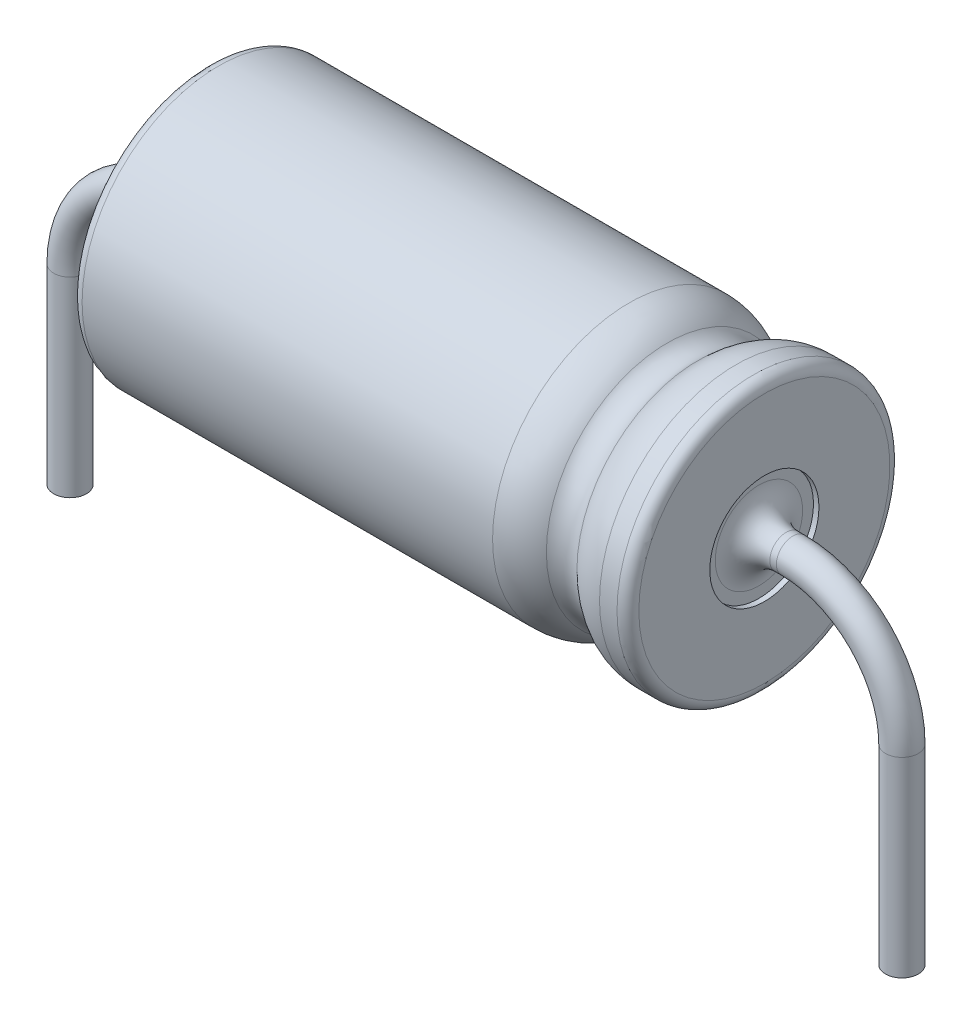
SolidWorks part; units mm, degrees
ref_plane "Front Plane" through (0, 0, 0) normal (0, 0, 1) x (1, 0, 0)
ref_plane "Top Plane" through (0, 0, 0) normal (0, 1, 0) x (1, 0, 0)
ref_plane "Right Plane" through (0, 0, 0) normal (1, 0, 0) x (0, 0, -1)
sketch "Sketch1" plane through (0, 0, 0) normal (0, 0, 1) x (1, 0, 0)
  line L1 (-7.62, 5) -> (-7.62, -3.3589) construction
  line L2 (-12.72, 5) -> (-2.52, 5)
  line L3 (-2.52, 2.5) -> (-27.3397, 2.5) construction
  line L4 (-2.52, 5) -> (-2.52, 2.5)
  line L5 (-12.72, 5) -> (-12.72, 2.5)
  dimension "D1" = 2.5
  dimension "D2" = 10.2
  dimension "D3" = 2.5
  dimension "D4" = 2.52
revolve "Base-Revolve-Thin" add sketch "Sketch1" angle 360 about L3
sketch "Sketch2" plane through (-2.52, 0, 0) normal (1, 0, 0) x (0, 0, -1)
  circle A0 centre (0, 2.5) radius 1
  dimension "D1" = 2
extrude "Cut-Extrude1" cut sketch "Sketch2" against normal blind 0.1
sketch "Sketch3" plane through (-12.72, 0, 0) normal (-1, 0, 0) x (0, 0, 1)
  circle A0 centre (0, 2.5) radius 1
  dimension "D1" = 2
extrude "Cut-Extrude2" cut sketch "Sketch3" against normal blind 0.1
fillet "Fillet1" radius 0.2 2 edges at (-2.52, 2.5, -2.5) (-12.72, 2.5, -2.5)
sketch "Sketch4" plane through (-2.62, 0, 0) normal (1, 0, 0) x (0, 0, -1)
  circle A0 centre (0, 2.5) radius 0.3
  dimension "D1" = 0.6
extrude "Boss-Extrude1" add sketch "Sketch4" along normal blind 0.62 and the other way blind 10.62
fillet "Fillet2" radius 0.5 2 edges at (-2.62, 2.5, -0.3) (-12.62, 2.2, 0)
sketch "Sketch5" plane through (0, 0, 0) normal (0, 0, 1) x (1, 0, 0)
  line L0 (0, 0.5) -> (0, -3)
  line L1 (-2.62, 2.5) -> (-2.52, 2.5) construction
  line L3 (-2, 2.2) -> (-2, 2.8) construction
  line L4 (0, 0.5) -> (-3.248, 0.5) construction
  line L5 (-7.62, 0) -> (-7.62, -2.8359) construction
  line L6 (-12.52, 0) -> (-2.72, 0) construction
  arc A0 (-2, 2.5) -> (0, 0.5) centre (-2, 0.5) cw
  dimension "D1" = 0.5
  dimension "D2" = 3
sketch "Sketch7" plane through (-2, 0, 0) normal (1, 0, 0) x (0, 0, -1)
  circle A1 centre (0, 2.5) radius 0.3
  circle A2 centre (0, 2.5) radius 0.3
  dimension "D1" = 0
sweep "Boss-Sweep2" add profiles "Sketch7" path "Sketch5"
ref_plane "Plane4" through (-7.62, 0, 0) normal (1, 0, 0) x (0, 0, -1)
mirror "Mirror1" about plane through (-7.62, 0, 0) normal (1, 0, 0) of "Boss-Sweep2"
sketch "Sketch8" plane through (0, 0, 0) normal (0, 0, 1) x (1, 0, 0)
  line L0 (-2.72, 5) -> (-12.52, 5) construction
  line L1 (-2.9791, 2.5) -> (-7.5151, 2.5) construction
  line L2 (-2.62, 2.5) -> (-2.52, 2.5) construction
  line L3 (-4.02, 5) -> (-4.02, 3.2058) construction
  line L4 (-2.52, 0.2) -> (-2.52, 4.8) construction
  line L5 (-3.0402, 5) -> (-4.9998, 5)
  arc A0 (-4.3, 4.7143) -> (-3.7401, 4.7143) centre (-4.02, 5) ccw
  arc A1 (-3.7401, 4.7143) -> (-3.0402, 5) centre (-3.0402, 4) cw
  arc A2 (-4.3, 4.7143) -> (-4.9998, 5) centre (-4.9998, 4) ccw
  dimension "D1" = 0.4
  dimension "D2" = 1
  dimension "D3" = 1.2201
  dimension "D4" = 0.2857
revolve "Cut-Revolve1" cut sketch "Sketch8" angle 360 about L1
ref_plane "Board Plane" through (0, -0.3, 0) normal (0, 1, 0) x (-1, 0, 0)
sketch "Component_Outline" plane through (0, -0.3, 0) normal (0, 1, 0) x (-1, 0, 0)
  line L0 (13.12, 0.3) -> (12.72, 0.5)
  line L1 (12.72, -1) -> (12.72, 1) construction
  line L2 (12.72, 0.5) -> (12.72, 2.5)
  line L3 (13.12, -0.3) -> (12.72, -0.5)
  line L4 (12.72, -2.3) -> (12.72, 2.3) construction
  line L5 (12.72, -0.5) -> (12.72, -2.5)
  line L6 (13.12, 0.3) -> (15.24, 0.3)
  line L7 (15.24, -0.3) -> (13.12, -0.3)
  line L8 (2.12, 0.3) -> (2.52, 0.5)
  line L9 (2.52, 2.3) -> (2.52, -2.3) construction
  line L10 (2.52, 0.5) -> (2.52, 2.5)
  line L11 (2.12, -0.3) -> (2.52, -0.5)
  line L12 (2.52, -0.5) -> (2.52, -2.5)
  line L13 (2.12, -0.3) -> (0, -0.3)
  line L14 (0, 0.3) -> (2.12, 0.3)
  line L15 (12.72, 2.5) -> (2.52, 2.5)
  line L16 (12.72, -2.5) -> (2.52, -2.5)
  line L17 (4.9998, -2.5) -> (12.52, -2.5) construction
  line L18 (12.52, 2.5) -> (4.9998, 2.5) construction
  arc A0 (12.62, 0.8) -> (13.12, 0.3) centre (13.12, 0.8) ccw construction
  arc A1 (13.12, -0.3) -> (12.62, -0.8) centre (13.12, -0.8) ccw construction
  arc A2 (15.24, 0.3) -> (15.24, -0.3) centre (15.24, 0) cw
  arc A3 (2.12, 0.3) -> (2.62, 0.8) centre (2.12, 0.8) ccw construction
  arc A4 (2.62, -0.8) -> (2.12, -0.3) centre (2.12, -0.8) ccw construction
  arc A5 (0, -0.3) -> (0, 0.3) centre (0, 0) cw
